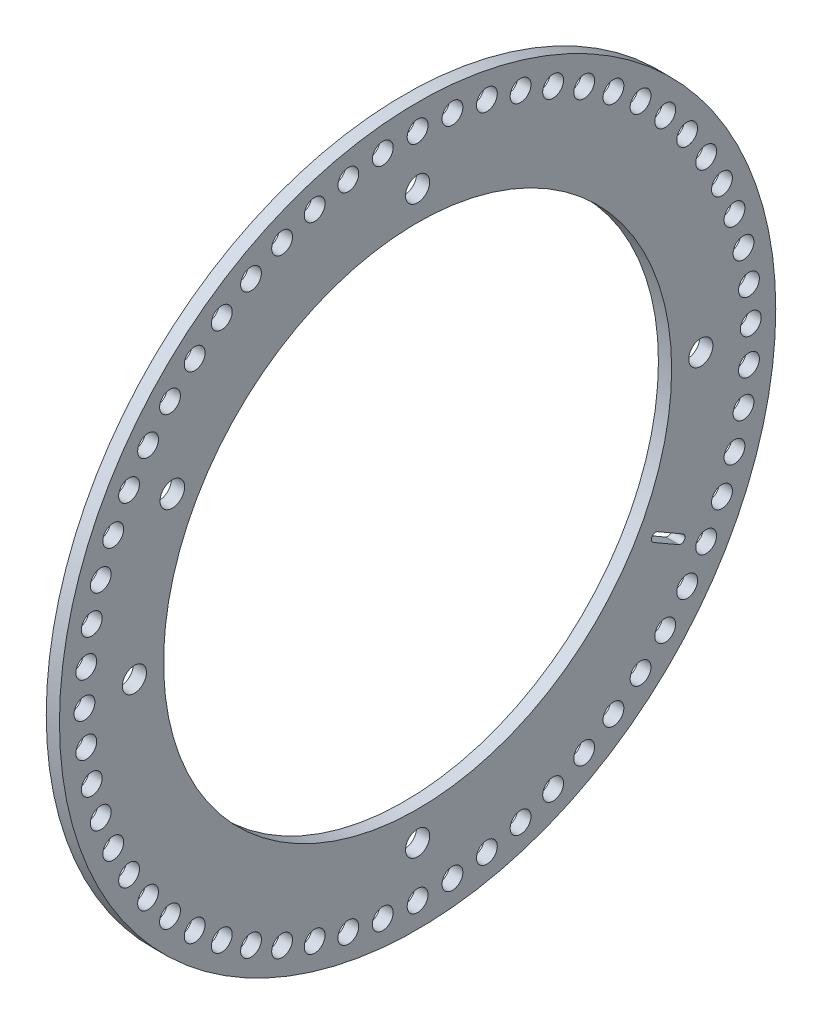
SolidWorks part; units mm, degrees
ref_plane "Front Plane" through (0, 0, 0) normal (0, 0, 1) x (1, 0, 0)
ref_plane "Top Plane" through (0, 0, 0) normal (0, 1, 0) x (1, 0, 0)
ref_plane "Right Plane" through (0, 0, 0) normal (1, 0, 0) x (0, 0, -1)
sketch "Sketch1" plane through (0, 0, 0) normal (1, 0, 0) x (0, 0, -1)
  circle A0 centre (0, 0) radius 43
  circle A1 centre (0, 0) radius 30.5
  dimension "D1" = 86
  dimension "D2" = 61
extrude "Boss-Extrude1" add sketch "Sketch1" along normal blind 1.5875
sketch "Sketch2" plane through (1.5875, 0, 0) normal (1, 0, 0) x (0, 0, -1)
  line L0 (-34.641, 20) -> (34.641, -20) construction
  circle A0 centre (0, 40) radius 1.25
  circle A1 centre (4.1811, 39.7809) radius 1.25
  circle A2 centre (8.3165, 39.1259) radius 1.25
  circle A3 centre (12.3607, 38.0423) radius 1.25
  circle A4 centre (16.2695, 36.5418) radius 1.25
  circle A50 centre (20, 34.641) radius 1.25
  circle A51 centre (23.5114, 32.3607) radius 1.25
  circle A52 centre (26.7652, 29.7258) radius 1.25
  circle A53 centre (29.7258, 26.7652) radius 1.25
  circle A54 centre (32.3607, 23.5114) radius 1.25
  circle A55 centre (34.641, 20) radius 1.25
  circle A56 centre (36.5418, 16.2695) radius 1.25
  circle A57 centre (38.0423, 12.3607) radius 1.25
  circle A58 centre (39.1259, 8.3165) radius 1.25
  circle A59 centre (39.7809, 4.1811) radius 1.25
  circle A60 centre (40, 0) radius 1.25
  circle A61 centre (39.7809, -4.1811) radius 1.25
  circle A62 centre (39.1259, -8.3165) radius 1.25
  circle A63 centre (38.0423, -12.3607) radius 1.25
  circle A64 centre (36.5418, -16.2695) radius 1.25
  circle A65 centre (34.641, -20) radius 1.25
  circle A66 centre (32.3607, -23.5114) radius 1.25
  circle A67 centre (29.7258, -26.7652) radius 1.25
  circle A68 centre (26.7652, -29.7258) radius 1.25
  circle A69 centre (23.5114, -32.3607) radius 1.25
  circle A70 centre (20, -34.641) radius 1.25
  circle A71 centre (16.2695, -36.5418) radius 1.25
  circle A72 centre (12.3607, -38.0423) radius 1.25
  circle A73 centre (8.3165, -39.1259) radius 1.25
  circle A74 centre (4.1811, -39.7809) radius 1.25
  circle A75 centre (0, -40) radius 1.25
  circle A76 centre (-4.1811, -39.7809) radius 1.25
  circle A77 centre (-8.3165, -39.1259) radius 1.25
  circle A78 centre (-12.3607, -38.0423) radius 1.25
  circle A79 centre (-16.2695, -36.5418) radius 1.25
  circle A80 centre (-20, -34.641) radius 1.25
  circle A81 centre (-23.5114, -32.3607) radius 1.25
  circle A82 centre (-26.7652, -29.7258) radius 1.25
  circle A83 centre (-29.7258, -26.7652) radius 1.25
  circle A84 centre (-32.3607, -23.5114) radius 1.25
  circle A85 centre (-34.641, -20) radius 1.25
  circle A86 centre (-36.5418, -16.2695) radius 1.25
  circle A87 centre (-38.0423, -12.3607) radius 1.25
  circle A88 centre (-39.1259, -8.3165) radius 1.25
  circle A89 centre (-39.7809, -4.1811) radius 1.25
  circle A90 centre (-40, 0) radius 1.25
  circle A91 centre (-39.7809, 4.1811) radius 1.25
  circle A92 centre (-39.1259, 8.3165) radius 1.25
  circle A93 centre (-38.0423, 12.3607) radius 1.25
  circle A94 centre (-36.5418, 16.2695) radius 1.25
  circle A95 centre (-34.641, 20) radius 1.25
  circle A96 centre (-32.3607, 23.5114) radius 1.25
  circle A97 centre (-29.7258, 26.7652) radius 1.25
  circle A98 centre (-26.7652, 29.7258) radius 1.25
  circle A99 centre (-23.5114, 32.3607) radius 1.25
  circle A100 centre (-20, 34.641) radius 1.25
  circle A101 centre (-16.2695, 36.5418) radius 1.25
  circle A102 centre (-12.3607, 38.0423) radius 1.25
  circle A103 centre (-8.3165, 39.1259) radius 1.25
  circle A104 centre (-4.1811, 39.7809) radius 1.25
  circle A105 centre (-29.4449, 17) radius 1.4776
  circle A106 centre (0, 0) radius 30.5 construction
  point P104 (0, 0)
  dimension "D1" = 2.5
  dimension "D2" = 40
  dimension "D4" = 34
  dimension "D3" = 60
extrude "Cut-Extrude1" cut sketch "Sketch2" against normal through all
sketch "Sketch3" plane through (1.5875, 0, 0) normal (1, 0, 0) x (0, 0, -1)
  circle A0 centre (0, 0) radius 34 construction
  point P3 (0, 34)
  point P4 (-34, 0)
  point P5 (0, -34)
  point P6 (34, 0)
  dimension "D1" = 68
hole_wizard "M2.5 Clearance Hole1" positions "Sketch4" profile "Sketch5" hole size "M2.5" standard "ANSI Metric"
sketch "Sketch4" plane through (1.5875, 0, 0) normal (1, 0, 0) x (0, 0, -1)
  point P0 (0, 34)
  point P3 (-34, 0)
  point P6 (34, 0)
  point P9 (0, -34)
sketch "Sketch5" plane through (1.5875, 34, 0) normal (0, 1, 0) x (0, 0, -1)
  line L0 (0, 0) -> (0, 6.8712)
  line L1 (0, 6.8712) -> (1.45, 6)
  line L2 (1.45, 6) -> (1.45, 0)
  line L5 (1.45, 0) -> (0, 0)
  line L10 (0, 6.8712) -> (-1.45, 6) construction
  line L11 (0, -6.35) -> (0, 107.95) construction
  dimension "Hole Dia." = 2.9
  dimension "Hole Depth" = 6
  dimension "Drill Angle" = 118
sketch "Sketch6" plane through (1.5875, 0, 0) normal (1, 0, 0) x (0, 0, -1)
  line L0 (-29.4449, 17) -> (0, 0) construction
  line L1 (0, 0) -> (37.2391, -21.5) construction
  line L2 (28.5788, -16.5) -> (28.8288, -16.067) construction
  line L3 (28.8288, -16.067) -> (31.8599, -17.817)
  line L4 (31.8599, -17.817) -> (31.3599, -18.683) construction
  line L5 (31.3599, -18.683) -> (28.3288, -16.933)
  line L6 (28.3288, -16.933) -> (28.5788, -16.5) construction
  circle A0 centre (0, 0) radius 43 construction
  arc A1 (28.3288, -16.933) -> (28.8288, -16.067) centre (28.5788, -16.5) cw
  arc A2 (31.8599, -17.817) -> (31.3599, -18.683) centre (31.6099, -18.25) cw
  dimension "D1" = 1
  dimension "D2" = 3.5
  dimension "D3" = 36.5
extrude "Cut-Extrude2" cut sketch "Sketch6" against normal through all
